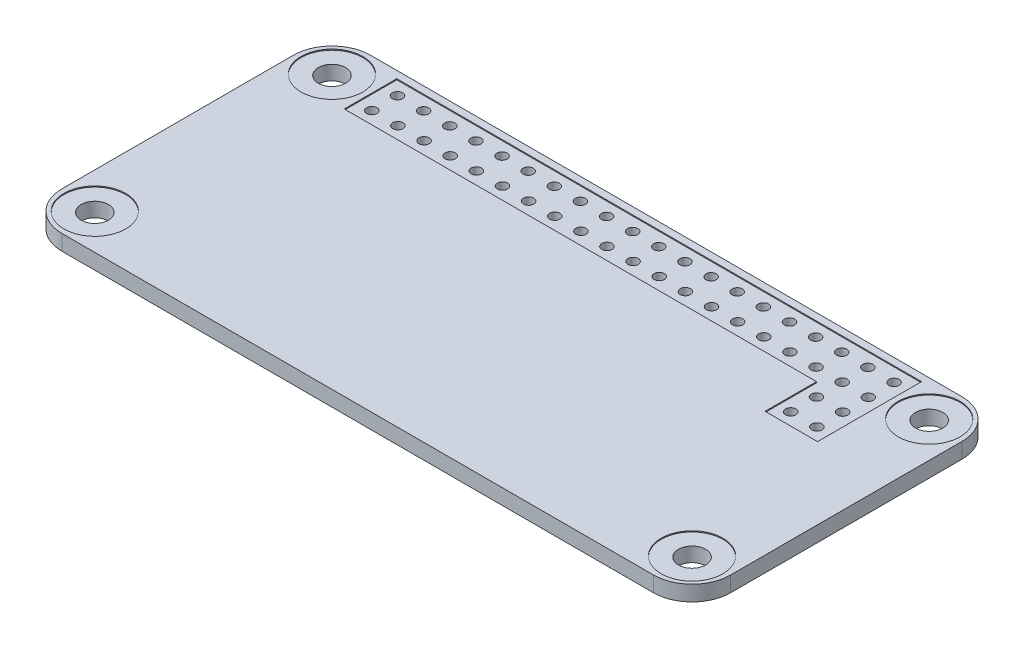
SolidWorks part; units mm, degrees
ref_plane "Front Plane" through (0, 0, 0) normal (0, 0, 1) x (1, 0, 0)
ref_plane "Top Plane" through (0, 0, 0) normal (0, 1, 0) x (1, 0, 0)
ref_plane "Right Plane" through (0, 0, 0) normal (1, 0, 0) x (0, 0, -1)
sketch "Sketch1" plane through (0, 0, 0) normal (0, 1, 0) x (1, 0, 0)
  line L1 (-28.75, 15) -> (28.75, 15)
  line L2 (-32.5, 11.25) -> (-32.5, -11.25)
  line L3 (-28.75, -15) -> (28.75, -15)
  line L4 (32.5, 11.25) -> (32.5, -11.25)
  line L5 (-32.5, 15) -> (32.5, -15) construction
  line L6 (-32.5, -15) -> (32.5, 15) construction
  arc A0 (-32.5, -11.25) -> (-28.75, -15) centre (-28.75, -11.25) ccw
  arc A1 (28.75, -15) -> (32.5, -11.25) centre (28.75, -11.25) ccw
  arc A2 (28.75, 15) -> (32.5, 11.25) centre (28.75, 11.25) cw
  arc A3 (-28.75, 15) -> (-32.5, 11.25) centre (-28.75, 11.25) ccw
  point P0 (0, 0)
  dimension "D3" = 3.75
  dimension "D1" = 65
  dimension "D2" = 30
extrude "Boss-Extrude1" add sketch "Sketch1" along normal blind 1.5 contours L1 A2 L4 A1 L3 A0 L2 A3
sketch "Sketch2" plane through (0, 1.5, 0) normal (0, 1, 0) x (1, 0, 0)
  line L0 (0, 15) -> (0, -15) construction
  line L1 (-28.75, 15) -> (28.75, 15) construction
  line L2 (-28.75, -15) -> (28.75, -15) construction
  line L3 (-32.5, 0) -> (32.5, 0) construction
  line L4 (-32.5, 11.25) -> (-32.5, -11.25) construction
  line L5 (32.5, 11.25) -> (32.5, -11.25) construction
  circle A0 centre (-29.025, 11.525) radius 1.325
  circle A2 centre (29.025, 11.525) radius 1.325
  circle A3 centre (29.025, -11.525) radius 1.325
  circle A4 centre (-29.025, -11.525) radius 1.325
  dimension "D1" = 2.65
  dimension "D2" = 2.15
  dimension "D3" = 2.15
extrude "Cut-Extrude1" cut sketch "Sketch2" against normal through all
sketch "Sketch3" plane through (0, 1.5, 0) normal (0, 1, 0) x (1, 0, 0)
  line L0 (-24.128, 13) -> (-24.128, 10.5) construction
  line L3 (-28.75, 15) -> (28.75, 15) construction
  line L5 (-32.5, 11.25) -> (-32.5, -11.25) construction
  circle A0 centre (-24.128, 13) radius 0.5
  circle A1 centre (-24.128, 10.5) radius 0.5
  dimension "D1" = 1
  dimension "D3" = 1.5
  dimension "D4" = 7.872
  dimension "D2" = 2.5
extrude "Cut-Extrude2" cut sketch "Sketch3" against normal through all
pattern_linear "LPattern1" count 20 spacing 2.54 along (1, 0, 0) of "Cut-Extrude2"
sketch "Sketch5" plane through (0, 1.5, 0) normal (0, 1, 0) x (1, 0, 0)
  line L0 (21.592, 10.5) -> (21.592, 5.5) construction
  line L1 (24.132, 10.5) -> (24.132, 5.5) construction
  line L2 (24.132, 5.5) -> (21.592, 5.5) construction
  circle A0 centre (21.592, 5.5) radius 0.5
  circle A1 centre (24.132, 5.5) radius 0.5
  circle A2 centre (21.592, 8) radius 0.5
  circle A3 centre (24.132, 8) radius 0.5
  dimension "D1" = 2.5
  dimension "D2" = 1
extrude "Cut-Extrude4" cut sketch "Sketch5" against normal through all
sketch "Sketch4" plane through (0, 1.5, 0) normal (0, 1, 0) x (1, 0, 0)
  line L0 (0, 0) -> (0, 14.3) construction
  line L1 (-24.128, 13) -> (-24.128, 10.5) construction
  line L2 (-25.5, 14.3) -> (25.5, 14.3)
  line L3 (-25.5, 14.3) -> (-25.5, 9.2)
  line L4 (-25.5, 9.2) -> (20.4, 9.2)
  line L5 (25.5, 14.3) -> (25.5, 9.2)
  line L6 (-25.5, 11.75) -> (-24.128, 11.75) construction
  line L7 (20.4, 9.2) -> (25.5, 9.2) construction
  line L8 (-2.5, -15) -> (-2.5, -11.55) construction
  line L9 (25.5, 9.2) -> (25.5, 4.2)
  line L10 (25.5, 4.2) -> (20.4, 4.2)
  line L11 (20.4, 9.2) -> (20.4, 4.2)
  line L12 (-28.75, -15) -> (28.75, -15) construction
  line L13 (-6.5, -11.55) -> (1.5, -11.55) construction
  line L14 (1.5, -11.55) -> (-1.575, -14.2) construction
  line L15 (-1.575, -14.2) -> (-1.575, -15) construction
  line L16 (-1.575, -15) -> (-3.425, -15) construction
  line L17 (-3.425, -15) -> (-3.425, -14.2) construction
  line L18 (-3.425, -14.2) -> (-6.5, -11.55) construction
  line L19 (-32.5, 11.25) -> (-32.5, -11.25) construction
  circle A0 centre (-29.025, 11.525) radius 3
  circle A1 centre (-29.025, -11.525) radius 3
  circle A2 centre (29.025, -11.525) radius 3
  circle A3 centre (29.025, 11.525) radius 3
  point P23 (-24.128, 11.75)
  point P26 (-25.5, 11.75)
  dimension "D1" = 6
  dimension "D2" = 5.1
  dimension "D3" = 51
  dimension "D4" = 5.1
  dimension "D5" = 5
  dimension "D6" = 8
  dimension "D7" = 1.85
  dimension "D8" = 3.45
  dimension "D9" = 0.8
  dimension "D10" = 30
extrude "Cut-Extrude3" cut sketch "Sketch4" against normal blind 0.1
